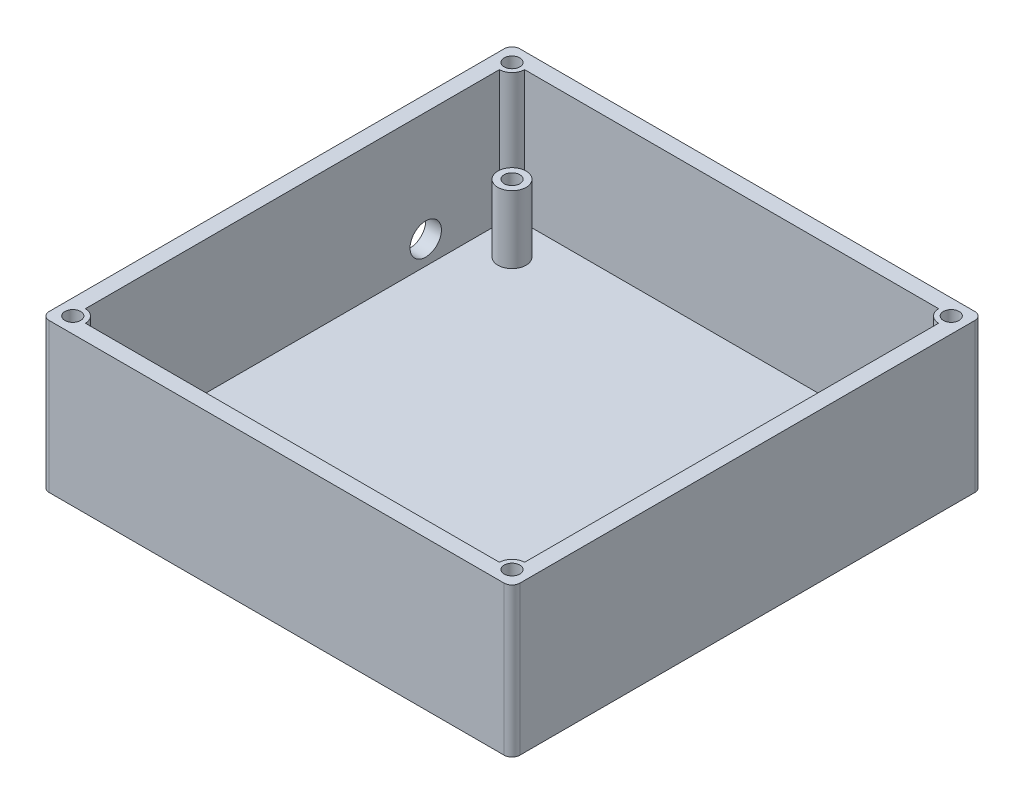
SolidWorks part; units mm, degrees
ref_plane "Спереди" through (0, 0, 0) normal (0, 0, 1) x (1, 0, 0)
ref_plane "Сверху" through (0, 0, 0) normal (0, 1, 0) x (1, 0, 0)
ref_plane "Справа" through (0, 0, 0) normal (1, 0, 0) x (0, 0, -1)
other "Configuration Table"
sketch "Эскиз1" plane through (0, 0, 0) normal (0, 1, 0) x (1, 0, 0)
  line L1 (-28, -28) -> (28, -28)
  line L2 (-28, -28) -> (-28, 28)
  line L3 (-28, 28) -> (28, 28)
  line L4 (28, -28) -> (28, 28)
  line L5 (0, 28) -> (0, -28) construction
  line L6 (-28, 0) -> (28, 0) construction
  point P0 (0, 0)
  dimension "D1" = 56
  dimension "D2" = 56
extrude "Бобышка-Вытянуть1" add sketch "Эскиз1" along normal blind 2
sketch "Эскиз2" plane through (0, 2, 0) normal (0, 1, 0) x (1, 0, 0)
  line L0 (0, 28) -> (0, -28) construction
  line L1 (28, 28) -> (-28, 28) construction
  line L2 (-28, -28) -> (28, -28) construction
  line L3 (-28, 0) -> (28, 0) construction
  line L4 (-28, 28) -> (-28, -28) construction
  line L5 (28, -28) -> (28, 28) construction
  circle A0 centre (-23.5, -23.5) radius 1.8
  circle A1 centre (-23.5, 23.5) radius 1.8
  circle A2 centre (23.5, 23.5) radius 1.8
  circle A3 centre (23.5, -23.5) radius 1.8
  dimension "D1" = 23.5
  dimension "do" = 23.5
  dimension "D2" = 23.5
  dimension "D3" = 23.5
  dimension "D4" = 23.5
  dimension "D5" = 23.5
  dimension "D6" = 23.5
  dimension "D7" = 23.5
extrude "Бобышка-Вытянуть2" add sketch "Эскиз2" along normal blind 8.6
sketch "Эскиз3" plane through (0, 10.6, 0) normal (0, 1, 0) x (1, 0, 0)
  line L0 (-23.5, 25.3) -> (-23.5, 21.7) construction
  line L1 (-25.3, 23.5) -> (-21.7, 23.5) construction
  line L2 (23.5, 25.2449) -> (23.5, 21.7) construction
  line L3 (21.7, 23.5) -> (25.3, 23.5) construction
  line L4 (23.5, -21.7) -> (23.5, -25.3) construction
  line L5 (21.7, -23.5) -> (25.3, -23.5) construction
  line L6 (-23.5, -21.7321) -> (-23.5, -25.3) construction
  line L7 (-25.2717, -23.5) -> (-21.7, -23.5) construction
  circle A0 centre (-23.5, 23.5) radius 1.8 construction
  circle A1 centre (-23.5, 23.5) radius 1.8 construction
  circle A2 centre (-23.5, 23.5) radius 1
  circle A3 centre (23.5, 23.5) radius 1.8 construction
  circle A4 centre (23.5, 23.5) radius 1.8 construction
  circle A5 centre (23.5, 23.4725) radius 1
  circle A6 centre (23.5, -23.5) radius 1.8 construction
  circle A7 centre (23.5, -23.5) radius 1.8 construction
  circle A8 centre (23.5, -23.5) radius 1
  circle A9 centre (-23.5, -23.5) radius 1.8 construction
  circle A10 centre (-23.5, -23.5) radius 1.8 construction
  circle A11 centre (-23.5, -23.5161) radius 1
extrude "Вырез-Вытянуть1" cut sketch "Эскиз3" against normal blind 8.6
sketch "Эскиз5" plane through (0, 0, 0) normal (0, -1, 0) x (1, 0, 0)
  line L1 (-28, -28) -> (30, -28)
  line L2 (-28, -28) -> (-28, -30)
  line L3 (-28, -30) -> (30, -30)
  line L4 (30, -28) -> (30, -30)
  line L5 (1, -30) -> (1, -28) construction
  line L6 (-28, -29) -> (30, -29) construction
  point P492 (1, -29)
  dimension "D1" = 58
  dimension "D2" = 2
extrude "Бобышка-Вытянуть3" add sketch "Эскиз5" against normal blind 19 separate body
sketch "Эскиз6" plane through (0, 0, 0) normal (0, -1, 0) x (1, 0, 0)
  line L1 (28, -28) -> (30, -28)
  line L2 (28, -28) -> (28, 30)
  line L3 (28, 30) -> (30, 30)
  line L4 (30, -28) -> (30, 30)
  line L5 (29, 30) -> (29, -28) construction
  line L6 (28, 1) -> (30, 1) construction
  point P272 (29, 1)
  dimension "D1" = 58
  dimension "D2" = 2
extrude "Бобышка-Вытянуть4" add sketch "Эскиз6" against normal blind 19
sketch "Эскиз7" plane through (0, 0, 0) normal (0, -1, 0) x (1, 0, 0)
  line L1 (28, 28) -> (-30, 28)
  line L2 (28, 28) -> (28, 30)
  line L3 (28, 30) -> (-30, 30)
  line L4 (-30, 28) -> (-30, 30)
  line L5 (-1, 30) -> (-1, 28) construction
  line L6 (28, 29) -> (-30, 29) construction
  point P164 (-1, 29)
  dimension "D1" = 2
  dimension "D2" = 58
extrude "Бобышка-Вытянуть5" add sketch "Эскиз7" against normal blind 19 separate body
sketch "Эскиз8" plane through (0, 0, 0) normal (0, -1, 0) x (1, 0, 0)
  line L1 (-28, 28) -> (-30, 28)
  line L2 (-28, 28) -> (-28, -30)
  line L3 (-28, -30) -> (-30, -30)
  line L4 (-30, 28) -> (-30, -30)
  line L5 (-29, -30) -> (-29, 28) construction
  line L6 (-28, -1) -> (-30, -1) construction
  point P416 (-29, -1)
  dimension "D1" = 2
  dimension "D2" = 58
extrude "Бобышка-Вытянуть6" add sketch "Эскиз8" against normal blind 19
sketch "Эскиз9" plane through (-30, 0, 0) normal (-1, 0, 0) x (0, 0, 1)
  line L0 (30, 0) -> (-30, 0) construction
  line L1 (-30, 19) -> (-30, 0) construction
  circle A0 centre (-17, 5) radius 2
  dimension "D1" = 4
  dimension "D2" = 5
  dimension "D3" = 13
extrude "Вырез-Вытянуть2" cut sketch "Эскиз9" against normal blind 2
sketch "Эскиз10" plane through (0, 2, 0) normal (0, 1, 0) x (1, 0, 0)
  circle A0 centre (-28, 28) radius 1.6
  circle A1 centre (28, 28) radius 1.6
  circle A2 centre (28, -28) radius 1.6
  circle A3 centre (-28, -28) radius 1.6
  dimension "D1" = 56
extrude "Бобышка-Вытянуть7" add sketch "Эскиз10" along normal blind 17
sketch "Эскиз11" plane through (0, 19, 0) normal (0, 1, 0) x (1, 0, 0)
  line L0 (0, 30) -> (0, -30.4053) construction
  line L1 (-30, 30) -> (30, 30) construction
  line L2 (-30, 0) -> (30, 0) construction
  line L3 (-30, -30) -> (-30, 30) construction
  line L4 (30, 30) -> (30, -30) construction
  circle A0 centre (-28, 28) radius 1
  circle A1 centre (28, 28) radius 1
  circle A2 centre (-28, -28) radius 1
  circle A3 centre (28, -28) radius 1
  dimension "mco" = 28
  dimension "D2" = 28
  dimension "D1" = 28
  dimension "D3" = 28
  dimension "D4" = 28
  dimension "D5" = 28
extrude "Вырез-Вытянуть3" cut sketch "Эскиз11" against normal blind 9
fillet "Скругление1" radius 1 4 edges at (-30, 9.5, -30) (30, 9.5, -30) (30, 9.5, 30) (-30, 9.5, 30)
equation "\"D1@Эскиз2\"=\"do\""
equation "\"D2@Эскиз2\"=\"do\""
equation "\"D3@Эскиз2\"=\"do\""
equation "\"D4@Эскиз2\"=\"do\""
equation "\"D5@Эскиз2\"=\"do\""
equation "\"D6@Эскиз2\"=\"do\""
equation "\"D7@Эскиз2\"=\"do\""
equation "\"D1@Эскиз4\"=\"s\""
equation "\"D2@Эскиз4\"=\"st\""
equation "\"D4@Эскиз4\"=\"s\""
equation "\"D5@Эскиз4\"=\"s\""
equation "\"D1@Эскиз5\"=\"s\""
equation "\"D2@Эскиз5\"=\"st\""
equation "\"D1@Эскиз6\"=\"s\""
equation "\"D2@Эскиз6\"=\"st\""
equation "\"D1@Эскиз7\"=\"st\""
equation "\"D2@Эскиз7\"=\"s\""
equation "\"D1@Эскиз8\"=\"st\""
equation "\"D2@Эскиз8\"=\"s\""
equation "\"D2@Эскиз11\"=\"mco\""
equation "\"D1@Эскиз11\"=\"mco\""
equation "\"D3@Эскиз11\"=\"mco\""
equation "\"D4@Эскиз11\"=\"mco\""
equation "\"D5@Эскиз11\"=\"mco\""
